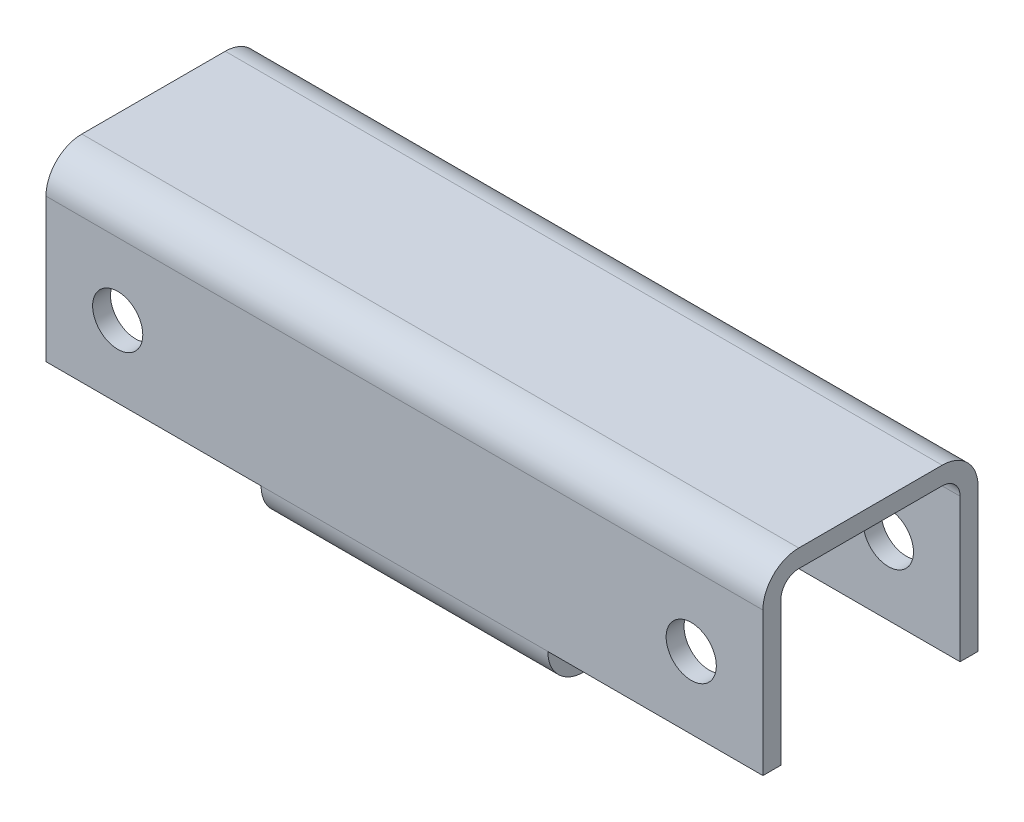
SolidWorks part; units mm, degrees
ref_plane "Plan de face" through (0, 0, 0) normal (0, 0, 1) x (1, 0, 0)
ref_plane "Plan de dessus" through (0, 0, 0) normal (0, 1, 0) x (1, 0, 0)
ref_plane "Plan de droite" through (0, 0, 0) normal (1, 0, 0) x (0, 0, -1)
sketch "Esquisse1" plane through (0, 0, 0) normal (0, 0, 1) x (1, 0, 0)
  line L0 (-100, 0) -> (100, 0)
other "Elément mécano-soudé1"
ref_plane "Plan1" through (-100, 0, 0) normal (1, 0, 0) x (0, 1, 0)
sketch "Sketch1" plane through (-100, 0, 0) normal (1, 0, 0) x (0, 1, 0)
  line L0 (-20, -25) -> (20, -25)
  line L1 (-25, -20) -> (-25, 20)
  line L2 (20, 25) -> (-20, 25)
  line L3 (25, 20) -> (25, -20)
  line L4 (-20, -30) -> (20, -30)
  line L5 (-30, -20) -> (-30, 20)
  line L6 (20, 30) -> (-20, 30)
  line L7 (30, 20) -> (30, -20)
  arc A0 (30, 20) -> (20, 30) centre (20, 20) ccw
  arc A1 (20, -30) -> (30, -20) centre (20, -20) ccw
  arc A2 (-30, -20) -> (-20, -30) centre (-20, -20) ccw
  arc A3 (-20, 30) -> (-30, 20) centre (-20, 20) ccw
  arc A4 (-20, 25) -> (-25, 20) centre (-20, 20) ccw
  arc A5 (25, 20) -> (20, 25) centre (20, 20) ccw
  arc A6 (20, -25) -> (25, -20) centre (20, -20) ccw
  arc A7 (-25, -20) -> (-20, -25) centre (-20, -20) ccw
  point P0 (-30, 0)
  point P1 (30, 0)
  point P2 (0, 30)
  point P3 (0, -30)
  point P4 (0, 0)
  point P5 (-30, -30)
  point P6 (30, -30)
  point P7 (30, 30)
  point P8 (-30, 30)
  point P33 (0, 0)
sketch "Esquisse2" plane through (-100, 0, 0) normal (1, 0, 0) x (0, 0, -1)
  line L1 (-30, -20) -> (30, -20)
  line L2 (-30, -20) -> (-30, -30)
  line L3 (-30, -30) -> (30, -30)
  line L4 (30, -20) -> (30, -30)
  line L5 (30, -20) -> (30, 20) construction
  line L6 (-30, 20) -> (-30, -20) construction
  line L7 (-20, -30) -> (20, -30) construction
extrude "Enlèv. mat.-Extru.1" cut sketch "Esquisse2" along normal blind 60
hole_wizard "Diamètre du perçage Ø14.0 (14)1" positions "Esquisse6" profile "Esquisse5" hole size "Ø14.0" standard "Ansi Metric" end condition through all
sketch "Esquisse6" plane through (0, 0, 30) normal (0, 0, 1) x (1, 0, 0)
  line L0 (-80, 0) -> (-100, 0) construction
  line L1 (-100, 20) -> (-100, -20) construction
  line L3 (80, 0) -> (100, 0) construction
  line L4 (100, 20) -> (100, -20) construction
  point P0 (-80, 0)
  point P2 (80, 0)
  dimension "D1" = 20
sketch "Esquisse5" plane through (-80, 0, 30) normal (1, 0, 0) x (0, -1, 0)
  line L0 (0, 0) -> (0, 60)
  line L1 (0, 60) -> (7, 60)
  line L2 (7, 60) -> (7, 0)
  line L5 (7, 0) -> (0, 0)
  line L11 (0, -6.35) -> (0, 107.95) construction
  dimension "Diamètre du perçage jusqu'au prochain" = 14
  dimension "Profondeur du perçage jusqu'au prochain" = 60
mirror "Symétrie1" about plane through (0, 0, 0) normal (1, 0, 0) of "Enlèv. mat.-Extru.1"
equation "\"D1@Sketch1\" = \"Thickness@Sketch1\"*2"
